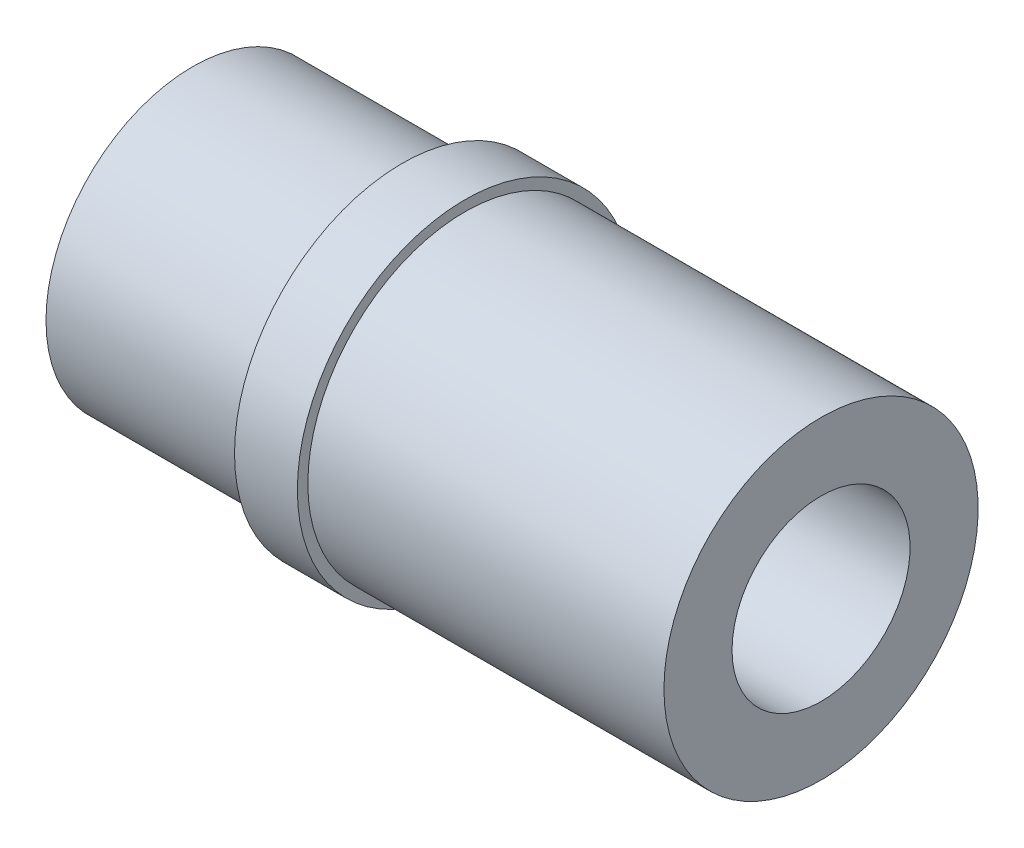
SolidWorks part; units mm, degrees
material "Plain Carbon Steel"
ref_plane "Front Plane" through (0, 0, 0) normal (0, 0, 1) x (1, 0, 0)
ref_plane "Top Plane" through (0, 0, 0) normal (0, 1, 0) x (1, 0, 0)
ref_plane "Right Plane" through (0, 0, 0) normal (1, 0, 0) x (0, 0, -1)
sketch "Sketch1" plane through (0, 0, 0) normal (0, 0, 1) x (1, 0, 0)
  line L0 (0, 4.25) -> (-21.1058, 4.25)
  line L1 (-21.1058, 4.25) -> (-30, 5.5)
  line L2 (-30, 5.5) -> (-30, 7)
  line L3 (-17, 7.5) -> (0, 7.5)
  line L4 (0, 7.5) -> (0, 4.25)
  line L5 (-108.7838, 0) -> (-17.0061, 0) construction
  line L6 (-20, 8) -> (-20, 7)
  line L7 (-20, 7) -> (-30, 7)
  line L8 (-17, 7.5) -> (-17, 8)
  line L9 (-17, 8) -> (-20, 8)
  dimension "D1" = 8
  dimension "D2" = 8.5
  dimension "D3" = 14
  dimension "D4" = 15
  dimension "D5" = 11
  dimension "D6" = 10
  dimension "D7" = 30
  dimension "D8" = 16
  dimension "D9" = 17
revolve "Revolve1" add sketch "Sketch1" angle 360 about L5
